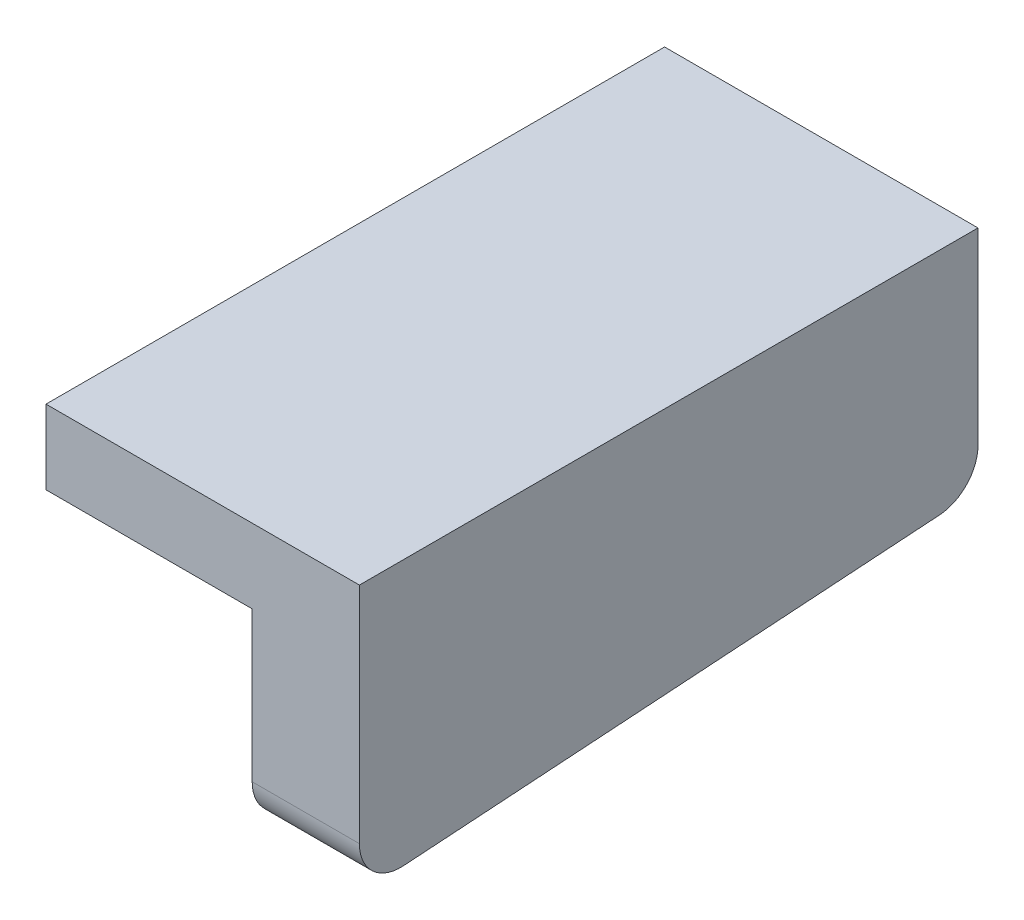
SolidWorks part; units mm, degrees
ref_plane "Front Plane" through (0, 0, 0) normal (0, 0, 1) x (1, 0, 0)
ref_plane "Top Plane" through (0, 0, 0) normal (0, 1, 0) x (1, 0, 0)
ref_plane "Right Plane" through (0, 0, 0) normal (1, 0, 0) x (0, 0, -1)
sketch "Sketch1" plane through (0, 0, 0) normal (0, 0, 1) x (1, 0, 0)
  line L5 (-6.3, 15.8) -> (1.3, 15.8)
  line L8 (1.3, 15.8) -> (1.3, 13.8)
  line L10 (1.3, 8.2) -> (1.3, 13.8)
  line L11 (-1.3, 8.2) -> (1.3, 8.2)
  line L12 (-1.3, 8.2) -> (-1.3, 14)
  line L13 (-6.3, 14) -> (-1.3, 14)
  line L14 (-6.3, 15.8) -> (-6.3, 14)
extrude "Boss-Extrude1" add sketch "Sketch1" along normal blind 15
sketch "Sketch3" plane through (1.3, 0, 0) normal (1, 0, 0) x (0, 0, -1)
  line L0 (-15, 9.3) -> (-15.8905, 6.8423)
  line L1 (-15, 8.2) -> (-15, 15.8) construction
  line L2 (-15, 9.3) -> (0, 10.3)
  line L3 (0, 8.2) -> (0, 15.8) construction
  line L4 (-15.8905, 6.8423) -> (2.0997, 7.0644)
  line L5 (2.0997, 7.0644) -> (0, 10.3)
extrude "Cut-Extrude1" cut sketch "Sketch3" against normal blind 15
fillet "Fillet1" radius 1 2 edges at (0, 10.3, 0) (0, 9.3, 15)
